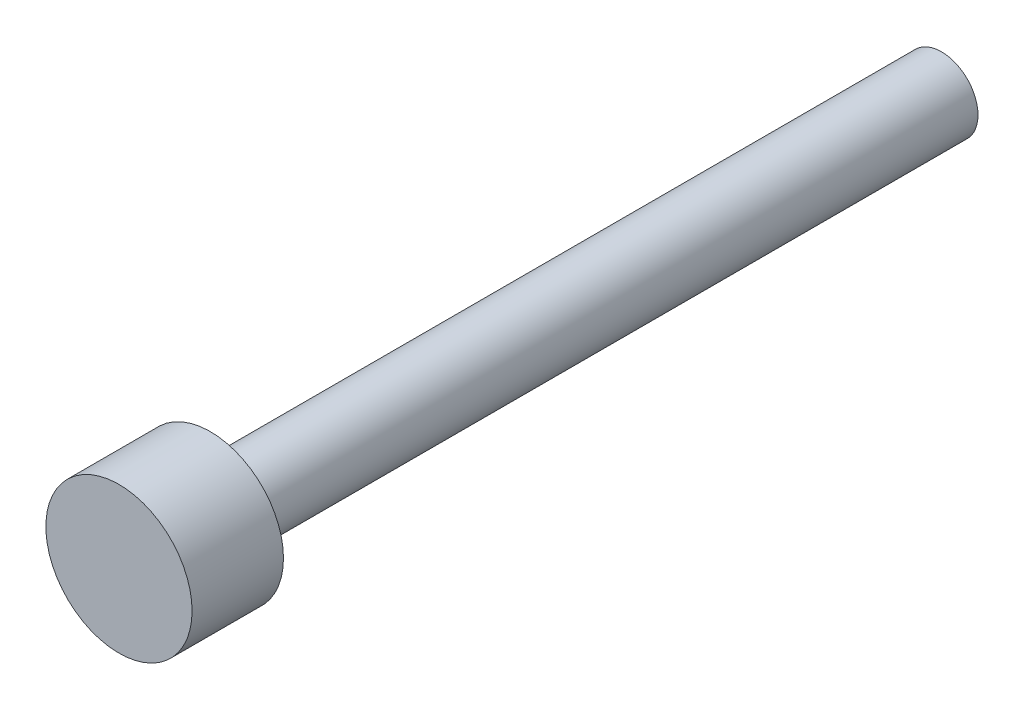
SolidWorks part; units mm, degrees
ref_plane "Plan de face" through (0, 0, 0) normal (0, 0, 1) x (1, 0, 0)
ref_plane "Plan de dessus" through (0, 0, 0) normal (0, 1, 0) x (1, 0, 0)
ref_plane "Plan de droite" through (0, 0, 0) normal (1, 0, 0) x (0, 0, -1)
sketch "Esquisse1" plane through (0, 0, 0) normal (0, 0, 1) x (1, 0, 0)
  circle A0 centre (0, 0) radius 4
  dimension "D1" = 8
extrude "Boss.-Extru.1" add sketch "Esquisse1" along normal blind 5
sketch "Esquisse2" plane through (0, 0, 0) normal (0, 0, 1) x (1, 0, 0)
  circle A0 centre (0, 0) radius 2
  dimension "D1" = 4
extrude "Boss.-Extru.2" add sketch "Esquisse2" against normal blind 40
